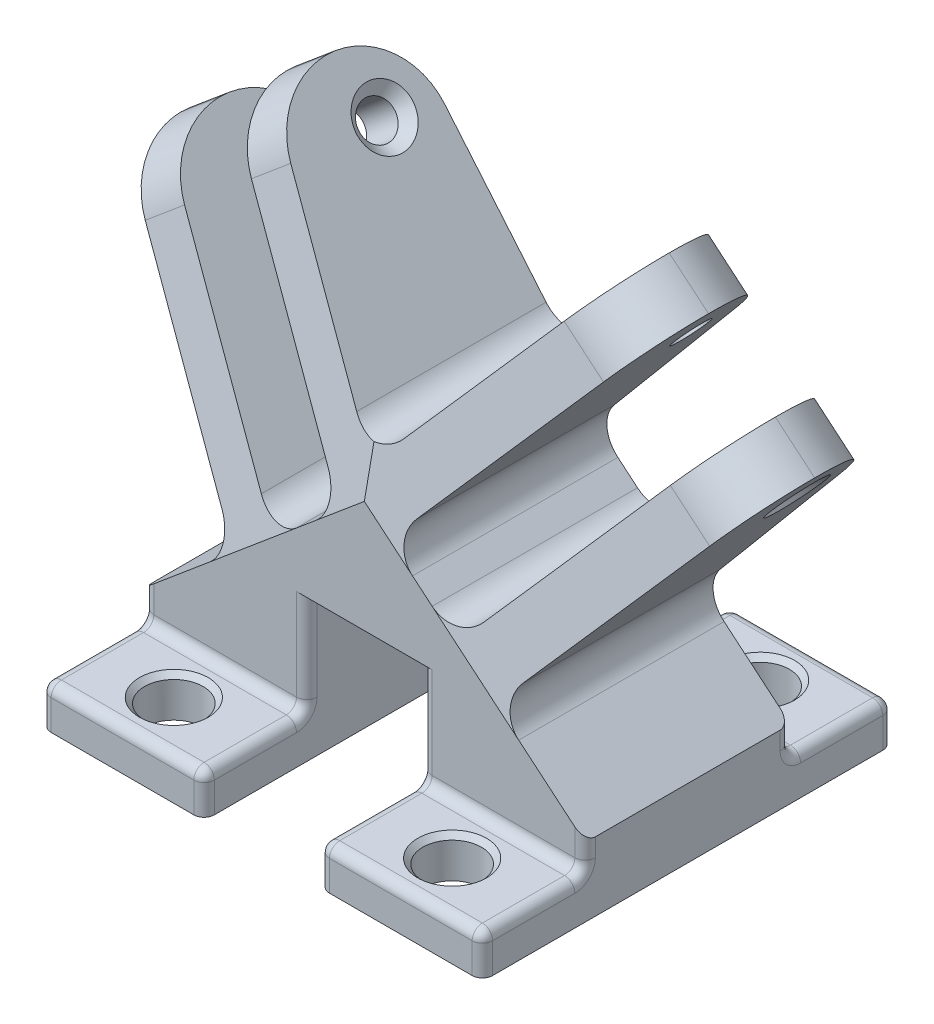
SolidWorks part; units mm, degrees
material "ABS"
ref_plane "Front Plane" through (0, 0, 0) normal (0, 0, 1) x (1, 0, 0)
ref_plane "Top Plane" through (0, 0, 0) normal (0, 1, 0) x (1, 0, 0)
ref_plane "Right Plane" through (0, 0, 0) normal (1, 0, 0) x (0, 0, -1)
sketch "Sketch1" plane through (0, 0, 0) normal (0, 0, 1) x (1, 0, 0)
  line L0 (0, 0) -> (-16.5, 0)
  line L1 (-16.5, 0) -> (0, 13.8451)
  line L2 (0, 13.8451) -> (0, 0) construction
  line L3 (0, 13.8451) -> (10, 13.8451)
  line L4 (5, 13.8451) -> (5, 0) construction
  line L5 (10, 0) -> (26.5, 0)
  line L6 (10, 13.8451) -> (10, 0) construction
  line L7 (26.5, 0) -> (10, 13.8451)
  line L8 (4.516, 13.8451) -> (-7.6475, 28.341) construction
  line L9 (-7.6475, 31.091) -> (-6.2588, 32.2563) construction
  line L10 (-10.3975, 28.341) -> (-11.7862, 27.1758) construction
  line L11 (-7.6475, 28.341) -> (-9.4152, 30.4477) construction
  line L12 (-7.6475, 28.341) -> (-9.7541, 26.5734) construction
  line L13 (-4.9393, 27.8635) -> (-3.5506, 29.0288) construction
  line L14 (-8.125, 25.6328) -> (-9.5138, 24.4675) construction
  line L15 (-11.7862, 27.1758) -> (-9.5138, 24.4675) construction
  line L16 (-3.5506, 29.0288) -> (-6.2588, 32.2563) construction
  line L17 (-15.5245, 44.3402) -> (6.7408, 17.8055)
  line L18 (-7.6475, 28.341) -> (-1.1361, 33.8047) construction
  line L19 (-9.4152, 30.4477) -> (-7.841, 31.7686) construction
  line L20 (-22.0358, 38.8766) -> (0.2294, 12.3418)
  line L21 (6.7408, 17.8055) -> (5, 19.8801)
  line L22 (0.2294, 12.3418) -> (-0.6056, 13.337)
  line L23 (0, 13.8451) -> (5, 18.0406)
  line L24 (5, 18.0406) -> (5, 19.8801)
  line L25 (26.5, 0) -> (10, 13.8451)
  line L26 (10, 13.8451) -> (5, 18.0406)
  line L27 (19.4152, 30.4477) -> (17.841, 31.7686) construction
  line L28 (17.6475, 31.091) -> (16.2588, 32.2563) construction
  line L29 (17.6475, 28.341) -> (11.1361, 33.8047) construction
  line L30 (13.5506, 29.0288) -> (16.2588, 32.2563) construction
  line L31 (14.9393, 27.8635) -> (13.5506, 29.0288) construction
  line L32 (18.125, 25.6328) -> (19.5138, 24.4675) construction
  line L33 (21.7862, 27.1758) -> (19.5138, 24.4675) construction
  line L34 (20.3975, 28.341) -> (21.7862, 27.1758) construction
  line L35 (17.6475, 28.341) -> (19.4152, 30.4477) construction
  line L36 (17.6475, 28.341) -> (19.7541, 26.5734) construction
  line L37 (5.484, 13.8451) -> (17.6475, 28.341) construction
  line L38 (9.7706, 12.3418) -> (10.6056, 13.337)
  line L39 (3.2592, 17.8055) -> (5, 19.8801)
  line L40 (25.5245, 44.3402) -> (3.2592, 17.8055)
  line L41 (32.0358, 38.8766) -> (9.7706, 12.3418)
  line L42 (-3.9064, 17.2707) -> (-19.8008, 3.9337)
  line L43 (-19.8008, 3.9337) -> (-16.5, 0)
  line L44 (29.8008, 3.9337) -> (26.5, 0)
  line L45 (13.9064, 17.2707) -> (29.8008, 3.9337)
  line L46 (-22.0358, 38.8766) -> (-25.8661, 35.6626)
  line L47 (-25.8661, 35.6626) -> (-7.7366, 14.0568)
  line L48 (-15.5245, 44.3402) -> (-11.6942, 47.5542)
  line L49 (-11.6942, 47.5542) -> (5, 27.6588)
  line L50 (5, 27.6588) -> (5, 19.8801)
  line L51 (35.8661, 35.6626) -> (17.7366, 14.0568)
  line L52 (32.0358, 38.8766) -> (35.8661, 35.6626)
  line L53 (21.6942, 47.5542) -> (5, 27.6588)
  line L54 (25.5245, 44.3402) -> (21.6942, 47.5542)
  line L55 (-3.9064, 17.2707) -> (2.605, 22.7344)
  line L56 (13.9064, 17.2707) -> (7.395, 22.7344)
  line L57 (-0.6056, 13.337) -> (-0.6056, 0)
  line L58 (10.6056, 13.337) -> (10.6056, 0)
  line L59 (0, 13.8451) -> (-0.6056, 13.8451)
  line L60 (-0.6056, 13.8451) -> (-0.6056, 13.337)
  line L61 (10, 13.8451) -> (10.6056, 13.8451)
  line L62 (10.6056, 13.8451) -> (10.6056, 13.337)
  circle A0 centre (-7.6475, 28.341) radius 2.75 construction
  circle A1 centre (17.6475, 28.341) radius 2.75 construction
  point P24 (-4.3918, 31.0729)
  point P65 (0, 0)
  dimension "D6" = 5.5
  dimension "D1" = 21.5392
  dimension "D2" = 40
  dimension "D3" = 10
  dimension "D4" = 0.484
  dimension "D5" = 18.923
  dimension "D7" = 7.5
  dimension "D8" = 14.5693
  dimension "D9" = 4.25
  dimension "D10" = 5
  dimension "D11" = 5
  dimension "D12" = 17.3193
  dimension "D13" = 15.8944
  dimension "D14" = 5.1351
extrude "Boss-Extrude1" add sketch "Sketch1" along normal blind 20 contours L2 L1 L0 | L5 L7 L25 L6 | L42 L43 L1 L22 | L46 L47 L42 L22 L20 | L55 L22 L1 L23 L24 L21 | L38 L56 L39 L24 L26 L25 | L3 L26 L23 | L50 L49 L48 L17 L21 | L40 L54 L53 L50 L39 | L52 L41 L38 L45 L51 | L45 L38 L7 L44
sketch "Sketch5" plane through (2.3816, 1.9984, 0) normal (-0.766, -0.6428, 0) x (0, 0, 1)
  line L0 (5.0261, 43.9455) -> (5.0261, 15.7411) construction
  line L1 (20, 43.9455) -> (0, 43.9455) construction
  line L2 (20, 15.7411) -> (0, 15.7411) construction
  line L3 (0, 43.9455) -> (0, 15.7411) construction
  line L4 (-0.55, 32.3762) -> (-0.55, 15.7411) construction
  circle A0 centre (5.0261, 38.1935) radius 1.75
  dimension "D3" = 3.5
  dimension "D1" = 5.5761
  dimension "D2" = 0.55
  dimension "D4" = 5.752
extrude "Cut-Extrude3" cut sketch "Sketch5" against normal through all
sketch3d "3DSketch1"
  line L0 (-0.6056, 13.8451, 20) -> (10.6056, 13.8451, 20) construction
  line L1 (-0.6056, 13.8451, 20) -> (10.6056, 13.8451, 20)
  point P2 (5, 13.8451, 20)
sketch "Sketch6" plane through (3.4867, -2.9257, 0) normal (0.766, -0.6428, 0) x (0, 0, -1)
  line L0 (-5.0261, 50.3734) -> (-5.0261, 22.169) construction
  line L1 (-20, 50.3734) -> (0, 50.3734) construction
  line L2 (-20, 22.169) -> (0, 22.169) construction
  line L3 (-20, 44.6214) -> (0, 44.6214) construction
  line L4 (-20, 50.3734) -> (-20, 22.169) construction
  line L5 (0, 50.3734) -> (0, 22.169) construction
  line L6 (0.55, 38.8041) -> (0.55, 22.169) construction
  circle A0 centre (-5.0261, 44.6214) radius 1.75
  dimension "D3" = 3.5
  dimension "D1" = 5.5761
  dimension "D2" = 5.752
  dimension "D4" = 0.55
extrude "Cut-Extrude4" cut sketch "Sketch6" against normal through all
sketch "Sketch7" plane through (2.3816, 1.9984, 0) normal (-0.766, -0.6428, 0) x (0, 0, 1)
  line L0 (20, 43.9455) -> (0, 43.9455) construction
  line L1 (0, 43.9455) -> (0, 15.7411) construction
  line L2 (20, 15.7411) -> (0, 15.7411) construction
  line L3 (13.8513, 38.6883) -> (20, 15.7411)
  line L4 (20, 43.9455) -> (20, 15.7411) construction
  line L6 (0, 36.9455) -> (0, 43.9455)
  line L9 (20, 43.9455) -> (20, 15.7411)
  arc A0 (7, 43.9455) -> (0, 36.9455) centre (7, 36.9455) ccw
  arc A1 (7, 43.9455) -> (13.8513, 38.6883) centre (7, 36.8525) cw
  line M3 (0, 43.9455) -> (0, 15.7411)
  line M5 (20, 15.7411) -> (20, 43.9455)
  line M6 (20, 43.9455) -> (0, 43.9455)
  dimension "D1" = 7
  dimension "D2" = 75
extrude "Cut-Extrude5" cut sketch "Sketch7" against normal through all contours A0 M6 M3 | A1 L3 M6 M5
sketch "Sketch8" plane through (3.4867, -2.9257, 0) normal (0.766, -0.6428, 0) x (0, 0, -1)
  line L0 (-20, 50.3734) -> (0, 50.3734) construction
  line L1 (0, 50.3734) -> (0, 22.169) construction
  line L2 (-13.8513, 45.1162) -> (-20, 22.169)
  line L4 (-20, 22.169) -> (-20, 50.3734)
  line L5 (-20, 50.3734) -> (-7, 50.3734)
  line L6 (-7, 50.3734) -> (0, 50.3734)
  line L7 (0, 50.3734) -> (0, 43.3734)
  line L8 (-20, 22.169) -> (0, 22.169) construction
  arc A0 (-7, 50.3734) -> (0, 43.3734) centre (-7, 43.3734) cw
  arc A1 (-7, 50.3734) -> (-13.8513, 45.1162) centre (-7, 43.2804) ccw
  line M3 (0, 22.169) -> (0, 50.3734)
  line M4 (0, 50.3734) -> (-20, 50.3734)
  line M5 (-20, 50.3734) -> (-20, 22.169)
  dimension "D1" = 7
  dimension "D2" = 75
extrude "Cut-Extrude6" cut sketch "Sketch8" against normal through all contours A1 L2 M4 M5 | A0 M4 M3
sketch "Sketch9" plane through (0, 0, 20) normal (0, 0, 1) x (1, 0, 0)
  line L0 (-0.6056, 0) -> (-16.5, 0) construction
  line L1 (-0.6056, 0) -> (-16.5, 0)
  line L2 (5, 13.8451) -> (5, 0) construction
  line L3 (-19.8008, 3.9337) -> (-16.5, 0) construction
  line L4 (-19.8008, 3.9337) -> (-16.5, 0)
  line L5 (-19.8008, 3.9337) -> (-0.6056, 3.9337)
  line L6 (-0.6056, 13.8451) -> (-0.6056, 0) construction
  line L7 (-0.6056, 3.9337) -> (-0.6056, 0)
  line L8 (10.6056, 3.9337) -> (10.6056, 0)
  line L9 (29.8008, 3.9337) -> (10.6056, 3.9337)
  line L10 (10.6056, 0) -> (26.5, 0)
  line L11 (29.8008, 3.9337) -> (26.5, 0)
  point P5 (-8.5528, 0)
extrude "Boss-Extrude3" add sketch "Sketch9" along normal blind 10
sketch "Sketch10" plane through (0, 3.9337, 0) normal (0, 1, 0) x (1, 0, 0)
  line L0 (-10.2032, -20) -> (-10.2032, -30) construction
  line L1 (-0.6056, -20) -> (-19.8008, -20) construction
  line L2 (-0.6056, -30) -> (-19.8008, -30) construction
  line L3 (-19.8008, -25) -> (-0.6056, -25) construction
  line L4 (-19.8008, -30) -> (-19.8008, -20) construction
  line L5 (-0.6056, -30) -> (-0.6056, -20) construction
  line L6 (5, -20) -> (5, -30) construction
  line L7 (-16.5, -30) -> (-0.6056, -30) construction
  line L8 (-16.5, -30) -> (-0.6056, -30)
  line L9 (-8.5528, -30) -> (-8.5528, -20) construction
  circle A1 centre (-8.5528, -25) radius 2.85
  circle A2 centre (18.5528, -25) radius 2.85
  dimension "D1" = 5.7
extrude "Cut-Extrude7" cut sketch "Sketch10" against normal through all contours A1 | A2
sketch "Sketch11" plane through (0, 0, 0) normal (0, 0, -1) x (-1, 0, 0)
  line L0 (19.8008, 3.9337) -> (16.5, 0) construction
  line L1 (0.6056, 0) -> (16.5, 0) construction
  line L2 (0.6056, 3.9337) -> (0.6056, 0) construction
  line L3 (19.8008, 3.9337) -> (0.6056, 3.9337) construction
  line L4 (-10.6056, 3.9337) -> (-10.6056, 0) construction
  line L5 (-10.6056, 0) -> (-26.5, 0) construction
  line L6 (-29.8008, 3.9337) -> (-26.5, 0) construction
  line L7 (-29.8008, 3.9337) -> (-10.6056, 3.9337) construction
  line L8 (19.8008, 3.9337) -> (16.5, 0)
  line L9 (0.6056, 0) -> (16.5, 0)
  line L10 (0.6056, 3.9337) -> (0.6056, 0)
  line L11 (19.8008, 3.9337) -> (0.6056, 3.9337)
  line L12 (-10.6056, 3.9337) -> (-10.6056, 0)
  line L13 (-10.6056, 0) -> (-26.5, 0)
  line L14 (-29.8008, 3.9337) -> (-26.5, 0)
  line L15 (-29.8008, 3.9337) -> (-10.6056, 3.9337)
extrude "Boss-Extrude4" add sketch "Sketch11" along normal blind 10
sketch "Sketch12" plane through (0, 3.9337, 0) normal (0, 1, 0) x (1, 0, 0)
  line L0 (-0.6056, 10) -> (-16.5, 10) construction
  line L1 (-0.6056, 10) -> (-16.5, 10)
  line L2 (-8.5528, 10) -> (-8.5528, 0) construction
  line L3 (-19.8008, 0) -> (-0.6056, 0) construction
  line L4 (5, -20) -> (5, -30) construction
  line L5 (5, -20) -> (5, -30)
  circle A0 centre (-8.5528, 5) radius 2.85
  circle A1 centre (18.5528, 5) radius 2.85
  dimension "D1" = 5.7
extrude "Cut-Extrude8" cut sketch "Sketch12" against normal through all contours L2 A0 | A1 | A0 L2
sketch "Sketch13" plane through (0, 0, 30) normal (0, 0, 1) x (1, 0, 0)
  line L0 (5, 13.8451) -> (5, 0) construction
  line L1 (-0.6056, 13.8451) -> (10.6056, 13.8451) construction
  line L3 (-16.5, 0) -> (-16.5, 3.9337)
  line L4 (-0.6056, 3.9337) -> (-19.8008, 3.9337) construction
  line L7 (-16.5, 3.9337) -> (-16.5, 6.7034)
  line L8 (-7.7366, 14.0568) -> (-19.8008, 3.9337) construction
  line L9 (-16.5, 6.7034) -> (-19.8008, 3.9337)
  line L10 (-19.8008, 3.9337) -> (-16.5, 0)
  line L11 (26.5, 0) -> (26.5, 3.9337)
  line L12 (29.8008, 3.9337) -> (26.5, 0)
  line L13 (26.5, 3.9337) -> (26.5, 6.7034)
  line L14 (26.5, 6.7034) -> (29.8008, 3.9337)
extrude "Cut-Extrude9" cut sketch "Sketch13" against normal through all
chamfer "Chamfer1" distance 1 angle 45 4 edges at (33.2936, 32.5969, 5.0261) (19.1218, 44.4885, 5.0261) (-21.0439, 29.9157, 5.0261) (-9.1218, 44.4885, 5.0261)
chamfer "Chamfer2" distance 0.5 angle 45 4 edges at (18.5528, 3.9337, 27.85) (18.5528, 3.9337, -2.15) (-8.5528, 3.9337, -2.15) (-8.5528, 3.9337, 27.85)
fillet "Fillet1" radius 1 32 edges at (26.5, 5.3186, 20) (10.6056, 8.8894, 20) (-0.6056, 8.8894, 20) (-16.5, 5.3186, 20) (26.5, 1.9669, 30) (26.5, 3.9337, 25) (18.5528, 3.9337, 30) (18.5528, 3.9337, 20) (10.6056, 1.9669, 30) (10.6056, 3.9337, 25) (-8.5528, 3.9337, 20) (-8.5528, 3.9337, 30) (-16.5, 3.9337, 25) (-16.5, 1.9669, 30) (-0.6056, 1.9669, 30) (-0.6056, 3.9337, 25) (26.5, 5.3186, 0) (10.6056, 8.8894, 0) (-0.6056, 8.8894, 0) (-16.5, 5.3186, 0) (26.5, 3.9337, -5) (26.5, 1.9669, -10) (18.5528, 3.9337, 0) (18.5528, 3.9337, -10) (10.6056, 1.9669, -10) (10.6056, 3.9337, -5) (-0.6056, 1.9669, -10) (-0.6056, 3.9337, -5) (-8.5528, 3.9337, -10) (-8.5528, 3.9337, 0) (-16.5, 1.9669, -10) (-16.5, 3.9337, -5)
fillet "Fillet2" radius 3 7 edges at (17.7366, 14.0568, 10) (5, 27.6588, 9.7009) (-3.9064, 17.2707, 10) (-7.7366, 14.0568, 10) (13.9064, 17.2707, 10) (7.395, 22.7344, 10) (2.605, 22.7344, 10)
sketch3d "3DSketch3"
  line L0 (-1.6056, 13.8451, 20) -> (11.6056, 13.8451, 20) construction
  line L1 (-1.6056, 13.8451, 20) -> (11.6056, 13.8451, 20)
  point P2 (5, 13.8451, 20)
sketch3d "3DSketch4"
  line L0 (18.763, 42.5051, 5.0261) -> (28.3385, 34.4703, 5.0261)
  circle A0 centre (18.763, 42.5051, 5.0261) radius 1.75 construction
  circle A1 centre (18.763, 42.5051, 5.0261) radius 1.75
  circle A4 centre (28.3385, 34.4703, 5.0261) radius 1.75 construction
  circle A5 centre (28.3385, 34.4703, 5.0261) radius 1.75
  point P2 (17.4224, 43.63, 5.0261)
  point P4 (17.4224, 43.63, 5.0261)
  point P8 (29.6791, 33.3454, 5.0261)
  point P10 (29.6791, 33.3454, 5.0261)
